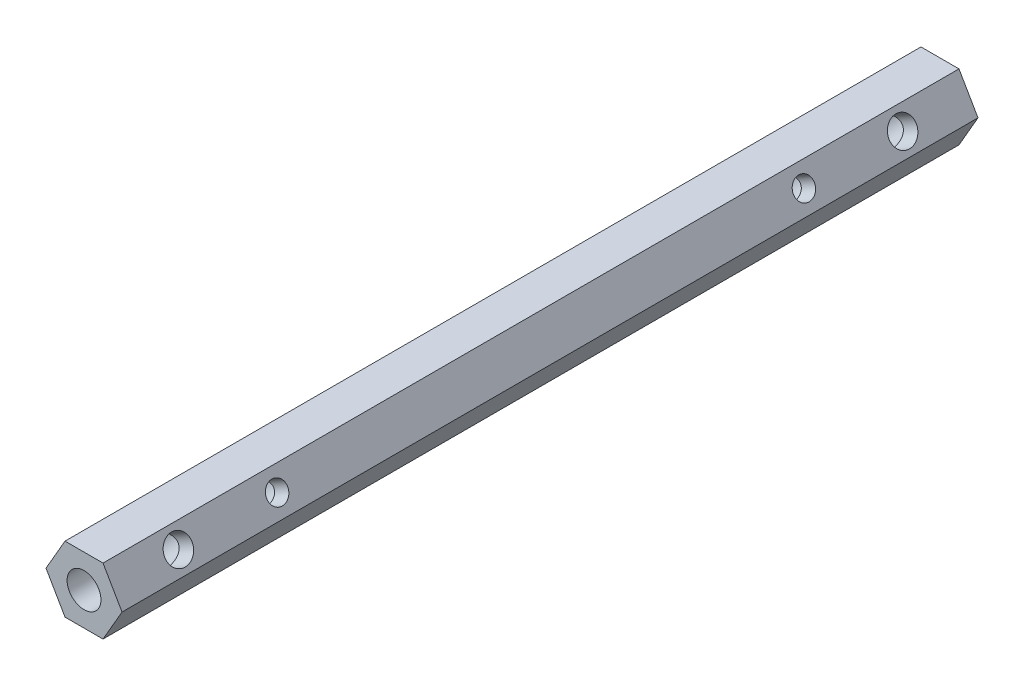
SolidWorks part; units mm, degrees
material "6061-T6 (SS)"
ref_plane "Front Plane" through (0, 0, 0) normal (0, 0, 1) x (1, 0, 0)
ref_plane "Top Plane" through (0, 0, 0) normal (0, 1, 0) x (1, 0, 0)
ref_plane "Right Plane" through (0, 0, 0) normal (1, 0, 0) x (0, 0, -1)
sketch "Sketch1" plane through (0, 0, 0) normal (0, 0, 1) x (1, 0, 0)
  line L1 (-3.6662, 6.35) -> (-7.3323, 0)
  line L2 (-7.3323, 0) -> (-3.6662, -6.35)
  line L3 (-3.6662, -6.35) -> (3.6662, -6.35)
  line L4 (3.6662, -6.35) -> (7.3323, 0)
  line L5 (7.3323, 0) -> (3.6662, 6.35)
  line L6 (3.6662, 6.35) -> (-3.6662, 6.35)
  circle A1 centre (0, 0) radius 3.2639
  circle A2 centre (0, 0) radius 6.35 construction
  dimension "D1" = 6.5278
  dimension "D2" = 12.7
extrude "Boss-Extrude1" add sketch "Sketch1" along normal blind 165.1
sketch "Sketch2" plane through (5.4993, 3.175, 0) normal (0.866, 0.5, 0) x (0, 0, -1)
  line L0 (0, 0) -> (-165.1, 0) construction
  line L1 (0, -3.6662) -> (0, 3.6662) construction
  line L2 (-165.1, -3.6662) -> (-165.1, 3.6662) construction
  line L3 (-82.55, 0) -> (-82.55, -15.3056) construction
  circle A0 centre (-31.75, 0) radius 2.0193
  circle A1 centre (-133.35, 0) radius 2.0193
  circle A2 centre (-12.7, 0) radius 2.6289
  circle A3 centre (-152.4, 0) radius 2.6289
  dimension "D1" = 4.0386
  dimension "D2" = 50.8
  dimension "D3" = 5.2578
  dimension "D4" = 12.7
extrude "Cut-Extrude1" cut sketch "Sketch2" against normal through all
